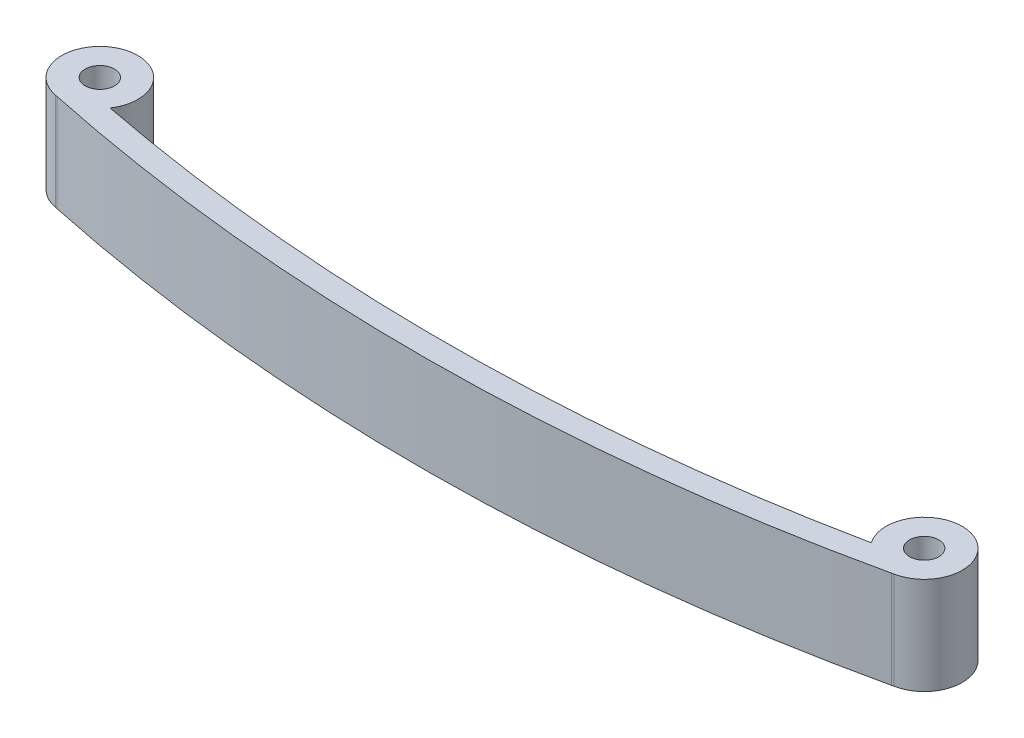
SolidWorks part; units mm, degrees
ref_plane "Front Plane" through (0, 0, 0) normal (0, 0, 1) x (1, 0, 0)
ref_plane "Top Plane" through (0, 0, 0) normal (0, 1, 0) x (1, 0, 0)
ref_plane "Right Plane" through (0, 0, 0) normal (1, 0, 0) x (0, 0, -1)
sketch "Sketch1" plane through (0, 0, 0) normal (0, 1, 0) x (1, 0, 0)
  line L0 (-35, 4.1426) -> (35, 4.5206) construction
  line L1 (35.4342, 1.2875) -> (35.6227, 1.3308)
  line L2 (-35.4132, 0.908) -> (-35.5757, 0.944)
  circle A0 centre (-35, 4.1426) radius 1.25
  circle A1 centre (35, 4.5206) radius 1.25
  arc A2 (-32.3092, 2.3199) -> (-35.5757, 0.944) centre (-35, 4.1426) ccw
  arc A3 (35.6227, 1.3308) -> (32.3291, 2.6689) centre (35, 4.5206) ccw
  arc A4 (-32.3092, 2.3199) -> (32.3291, 2.6689) centre (-0.865, 164.5106) ccw
  arc A5 (-35.4132, 0.908) -> (35.4342, 1.2875) centre (-0.865, 164.5106) ccw
  arc A7 (-35, 2.8648) -> (35, 3.2398) centre (-0.865, 164.5106) ccw construction
  circle A8 centre (-35, 4.1426) radius 3.25 construction
  circle A9 centre (35, 4.5206) radius 3.25 construction
  point P7 (38.108, 5.4708)
  point P18 (-31.892, 5.0928)
  dimension "D1" = 2.5
  dimension "D2" = 2.5
  dimension "D3" = 70
  dimension "D4" = 35
  dimension "D5" = 2
  dimension "D7" = 2
extrude "Boss-Extrude1" add sketch "Sketch1" along normal blind 8.3
